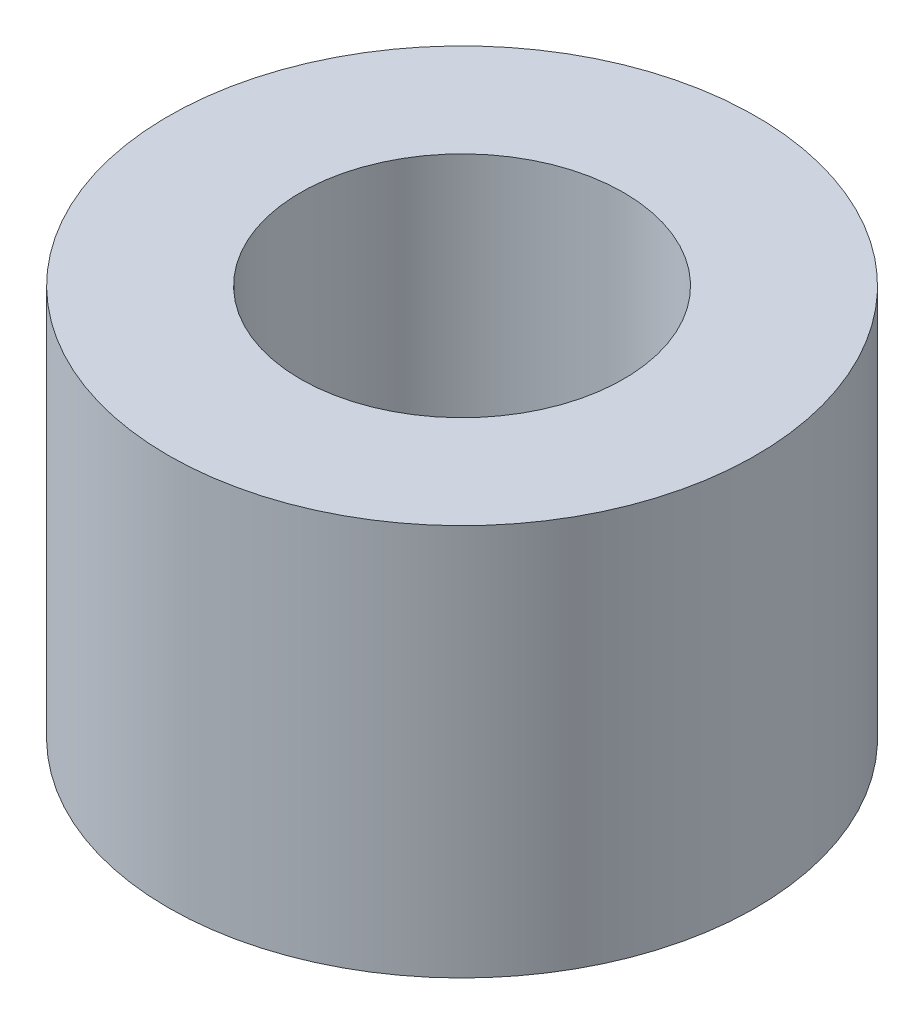
SolidWorks part; units mm, degrees
ref_plane "Спереди" through (0, 0, 0) normal (0, 0, 1) x (1, 0, 0)
ref_plane "Сверху" through (0, 0, 0) normal (0, 1, 0) x (1, 0, 0)
ref_plane "Справа" through (0, 0, 0) normal (1, 0, 0) x (0, 0, -1)
sketch "Sketch1" plane through (0, 0, 0) normal (0, 1, 0) x (1, 0, 0)
  circle A0 centre (0, 0) radius 1.65
  circle A1 centre (0, 0) radius 3
  dimension "D1" = 3.3
  dimension "D2" = 6
extrude "Boss-Extrude1" add sketch "Sketch1" along normal blind 4
